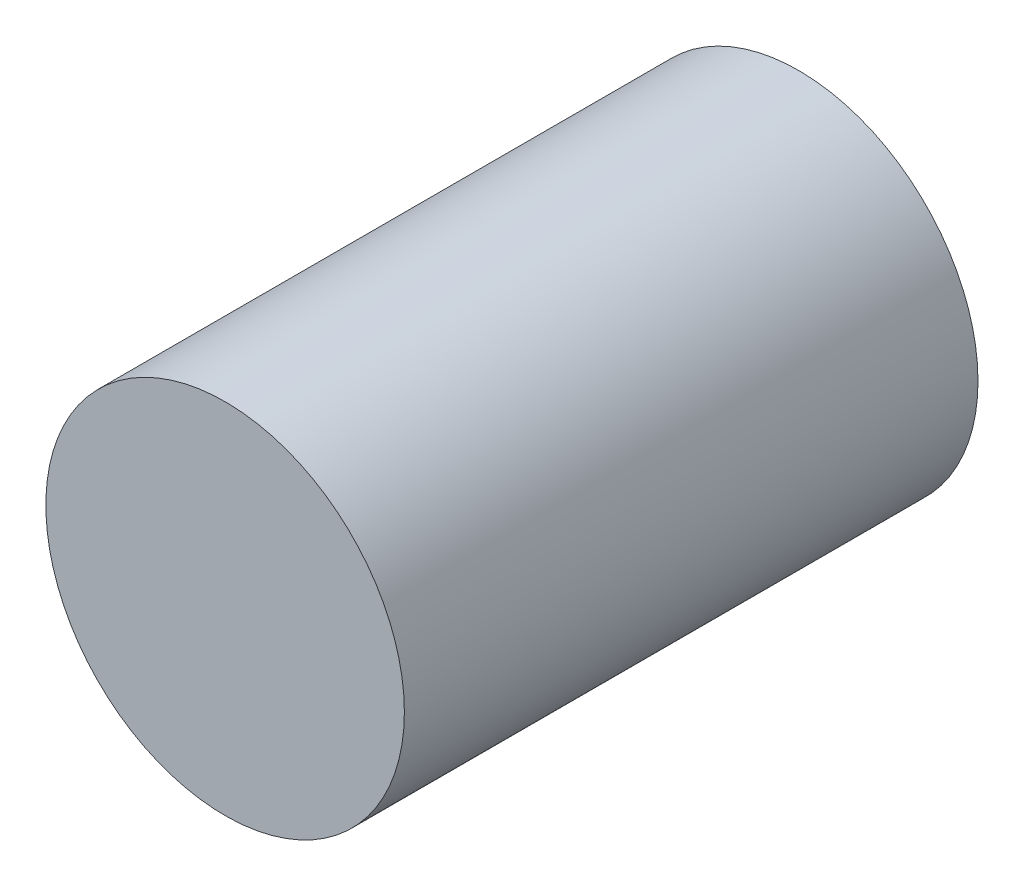
SolidWorks part; units mm, degrees
ref_plane "前视基准面" through (0, 0, 0) normal (0, 0, 1) x (1, 0, 0)
ref_plane "上视基准面" through (0, 0, 0) normal (0, 1, 0) x (1, 0, 0)
ref_plane "右视基准面" through (0, 0, 0) normal (1, 0, 0) x (0, 0, -1)
other "Configuration Table"
sketch "草图1" plane through (0, 0, 0) normal (0, 0, 1) x (1, 0, 0)
  circle A0 centre (0, 0) radius 25
  dimension "D1" = 50
extrude "凸台-拉伸1" add sketch "草图1" along normal blind 80
